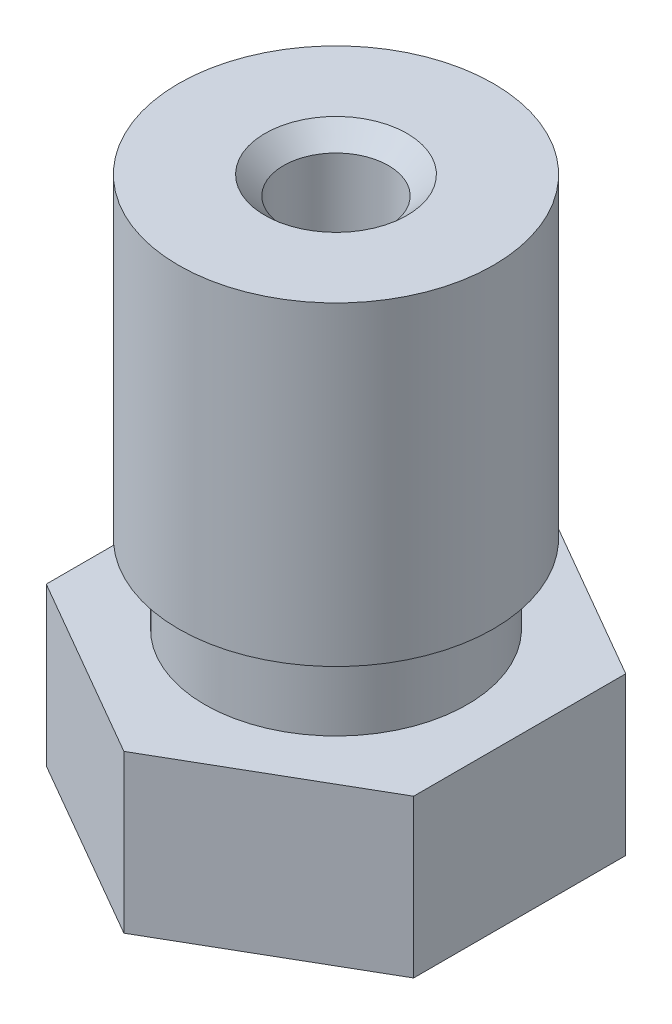
SolidWorks part; units mm, degrees
material "Brass"
ref_plane "Front Plane" through (0, 0, 0) normal (0, 0, 1) x (1, 0, 0)
ref_plane "Top Plane" through (0, 0, 0) normal (0, 1, 0) x (1, 0, 0)
ref_plane "Right Plane" through (0, 0, 0) normal (1, 0, 0) x (0, 0, -1)
sketch "Sketch1" plane through (0, 0, 0) normal (0, 1, 0) x (1, 0, 0)
  line L1 (0, 4.0415) -> (-3.5, 2.0207)
  line L2 (-3.5, 2.0207) -> (-3.5, -2.0207)
  line L3 (-3.5, -2.0207) -> (0, -4.0415)
  line L4 (0, -4.0415) -> (3.5, -2.0207)
  line L5 (3.5, -2.0207) -> (3.5, 2.0207)
  line L6 (3.5, 2.0207) -> (0, 4.0415)
  circle A0 centre (0, 0) radius 3.5 construction
  dimension "D1" = 7
extrude "Boss-Extrude1" add sketch "Sketch1" along normal blind 12.5
sketch "Sketch2" plane through (0, 0, 0) normal (0, 0, 1) x (1, 0, 0)
  line L0 (0, 0) -> (0, 13.417) construction
  line L1 (0, 0) -> (0, -1.6554) construction
  line L2 (-1.3536, 12.5) -> (-1, 12.1464)
  line L3 (-1, 12.1464) -> (-1, 2)
  line L4 (-1, 2) -> (-0.75, 1.75)
  line L5 (-0.75, 1.75) -> (-0.75, 1.05)
  line L6 (-0.75, 1.05) -> (-0.2, 0.5)
  line L7 (-0.2, 0.5) -> (-0.2, 0)
  line L8 (0, 12.5) -> (-1.3536, 12.5) construction
  line L9 (0, 0) -> (-5.5573, 0) construction
  line L10 (-0.2, 0) -> (0, 0)
  line L11 (-0.5, 0) -> (-1.9004, 2)
  line L12 (-1.9004, 2) -> (-4.5393, 2)
  line L13 (-4.5393, 2) -> (-4.5393, 5)
  line L14 (-4.5393, 5) -> (-2.5, 5)
  line L15 (-2.5, 5) -> (-2.5, 6.2113)
  line L16 (-2.5, 6.2113) -> (-3, 6.5)
  line L17 (-3, 6.5) -> (-3, 12.5)
  line L19 (-3, 12.5) -> (-7.5282, 12.5)
  line L20 (-7.5282, 12.5) -> (-7.5282, 0)
  line L21 (-7.5282, 0) -> (-0.5, 0)
  line L22 (0, 0) -> (0, 12.5)
  line L23 (0, 12.5) -> (-1.3536, 12.5)
  dimension "D1" = 12.5
  dimension "D2" = 0.5
  dimension "D3" = 10.5
  dimension "D4" = 2
  dimension "D5" = 1.5
  dimension "D6" = 0.4
  dimension "D7" = 125
  dimension "D8" = 0.5
  dimension "D9" = 6
  dimension "D10" = 6
  dimension "D11" = 5
  dimension "D12" = 60
  dimension "D15" = 0.7
  dimension "D16" = 45
revolve "Cut-Revolve1" cut sketch "Sketch2" angle 360 about L22
